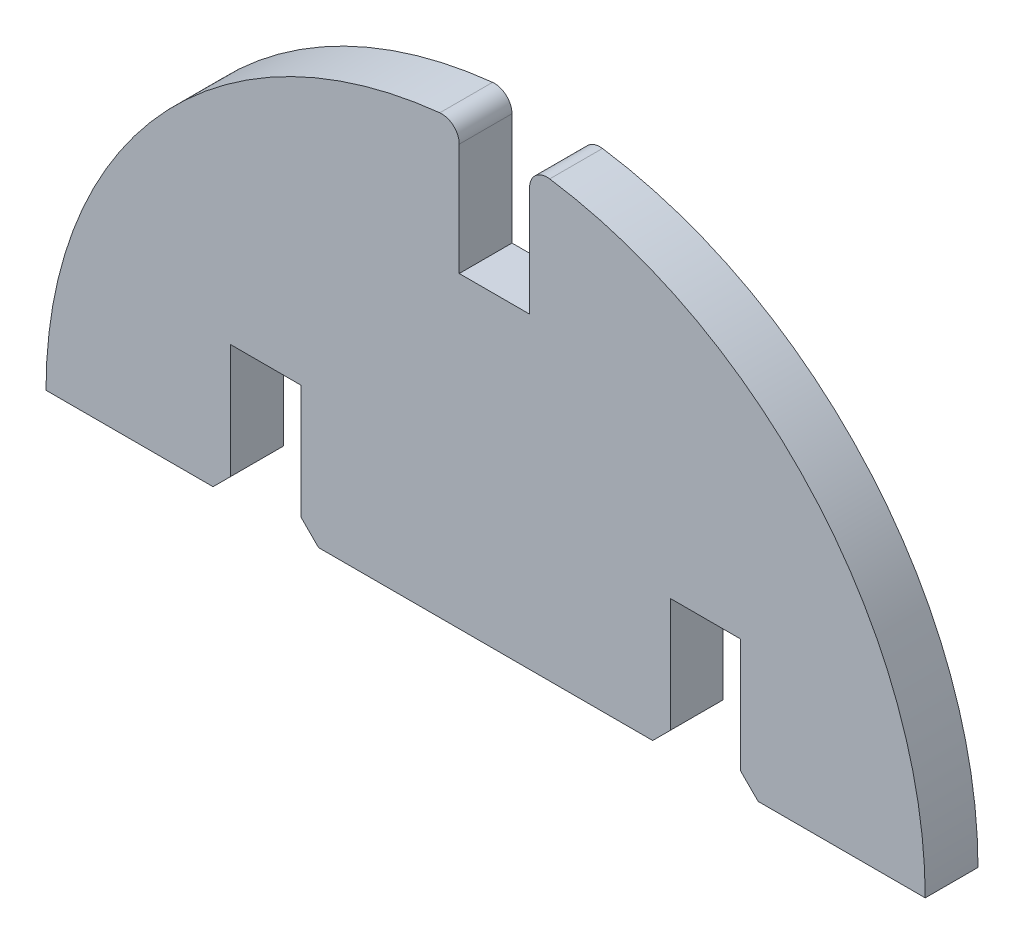
SolidWorks part; units mm, degrees
ref_plane "Front Plane" through (0, 0, 0) normal (0, 0, 1) x (1, 0, 0)
ref_plane "Top Plane" through (0, 0, 0) normal (0, 1, 0) x (1, 0, 0)
ref_plane "Right Plane" through (0, 0, 0) normal (1, 0, 0) x (0, 0, -1)
sketch "Sketch1" plane through (0, 0, 0) normal (0, 0, 1) x (1, 0, 0)
  line L0 (-25, 0) -> (-15.5, 0)
  line L1 (-9.5, 0) -> (9.5, 0)
  line L2 (-14.5, 7.5) -> (-10.5, 7.5)
  line L3 (-14.5, 7.5) -> (-14.5, 1)
  line L4 (-12.5, 0) -> (-12.5, 7.5) construction
  line L5 (-10.5, 7.5) -> (-10.5, 1)
  line L6 (-15.5, 0) -> (-14.5, 1)
  line L7 (-10.5, 1) -> (-9.5, 0)
  line L8 (10.5, 7.5) -> (14.5, 7.5)
  line L9 (10.5, 7.5) -> (10.5, 1)
  line L10 (14.5, 7.5) -> (14.5, 1)
  line L11 (9.5, 0) -> (10.5, 1)
  line L12 (14.5, 1) -> (15.5, 0)
  line L13 (15.5, 0) -> (25, 0)
  line L14 (0, 25) -> (0, 0) construction
  line L16 (-1.5, 23.8694) -> (-1.5, 17.5)
  line L17 (-1.5, 17.5) -> (2.5, 17.5)
  line L18 (2.5, 23.7434) -> (2.5, 17.5)
  arc A0 (25, 0) -> (3.6458, 24.7327) centre (0, 0) ccw
  arc A1 (-2.6042, 24.864) -> (-25, 0) centre (0, 0) ccw
  arc A2 (2.5, 23.7434) -> (3.6458, 24.7327) centre (3.5, 23.7434) cw
  arc A3 (-1.5, 23.8694) -> (-2.6042, 24.864) centre (-2.5, 23.8694) ccw
  point P1 (-12.5, 0)
  point P7 (-10.5, 0)
  point P10 (-14.5, 0)
  point P15 (0, 25)
  point P31 (-1.5, 24.955)
  dimension "D1" = 12.5
  dimension "D4" = 1
  dimension "D2" = 50
  dimension "D5" = 4
  dimension "D6" = 4
  dimension "D3" = 2
extrude "Boss-Extrude1" add sketch "Sketch1" along normal blind 3 contours A1 L0 L6 L3 L2 L5 L7 L1 L11 L9 L8 L10 L12 L13 A0 A2 L18 L17 L16 A3
